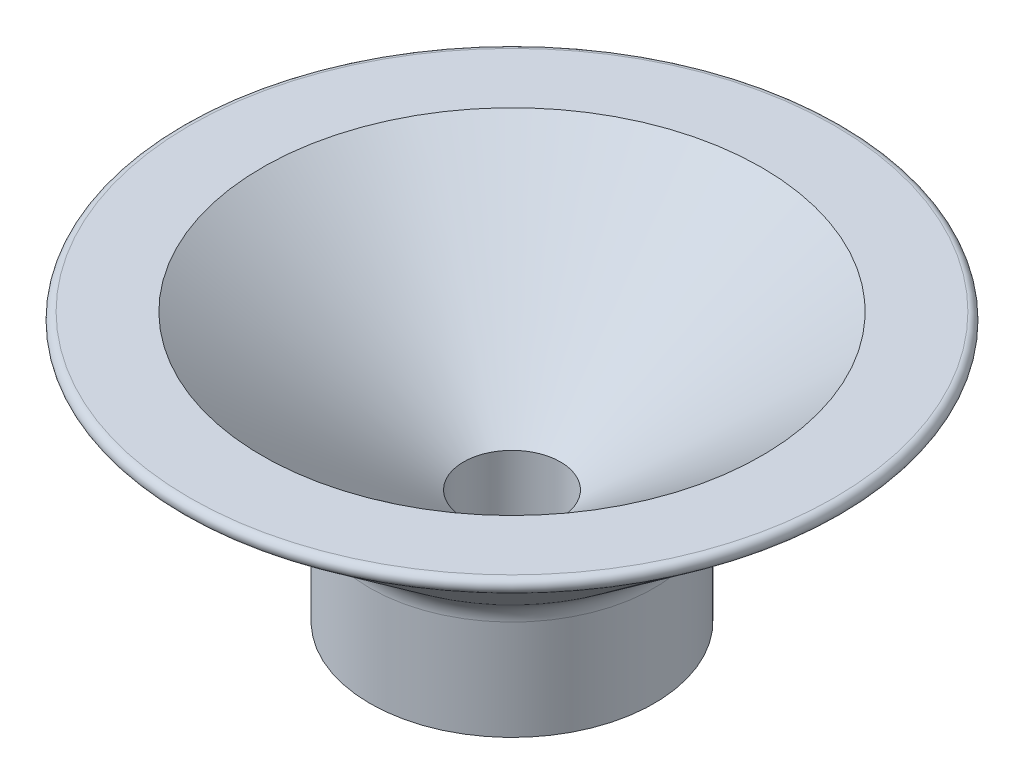
SolidWorks part; units mm, degrees
material "PLA"
ref_plane "Front Plane" through (0, 0, 0) normal (0, 0, 1) x (1, 0, 0)
ref_plane "Top Plane" through (0, 0, 0) normal (0, 1, 0) x (1, 0, 0)
ref_plane "Right Plane" through (0, 0, 0) normal (1, 0, 0) x (0, 0, -1)
sketch "Sketch1" plane through (0, 0, 0) normal (0, 0, 1) x (1, 0, 0)
  line L0 (-1.7, 0) -> (-4.9869, 0)
  line L1 (-4.9869, 0) -> (-12.0508, 5.4164)
  line L2 (-12.0508, 5.4164) -> (-8.7639, 5.4164)
  line L3 (-8.7639, 5.4164) -> (-1.7, 0)
  line L4 (0, 0) -> (0, 21.8983) construction
  dimension "D1" = 5.4164
  dimension "D2" = 8.7639
  dimension "D3" = 2
  dimension "D4" = 1.7
revolve "Revolve1" add sketch "Sketch1" angle 360 about L4
sketch "Sketch2" plane through (0, 0, 0) normal (0, -1, 0) x (1, 0, 0)
  circle A1 centre (0, 0) radius 4.9869
  circle A2 centre (0, 0) radius 4.9869
  circle A3 centre (0, 0) radius 1.7
  dimension "D2" = 3.4
  dimension "D1" = 0
extrude "Boss-Extrude1" add sketch "Sketch2" along normal blind 4
fillet "Fillet1" radius 0.25 1 edges at (0, 5.4164, -12.0508)
fillet "Fillet2" radius 1 1 edges at (0, 0, -4.9869)
sketch "Sketch4" plane through (0, 0, 0) normal (0, 0, 1) x (1, 0, 0)
  line L0 (0, 0) -> (0, -4) construction
  line L1 (-4.9869, -4) -> (4.9869, -4) construction
  line L2 (-8.7639, 5.4164) -> (0, 0) construction
  line L3 (0, 0) -> (8.7639, 5.4164) construction
